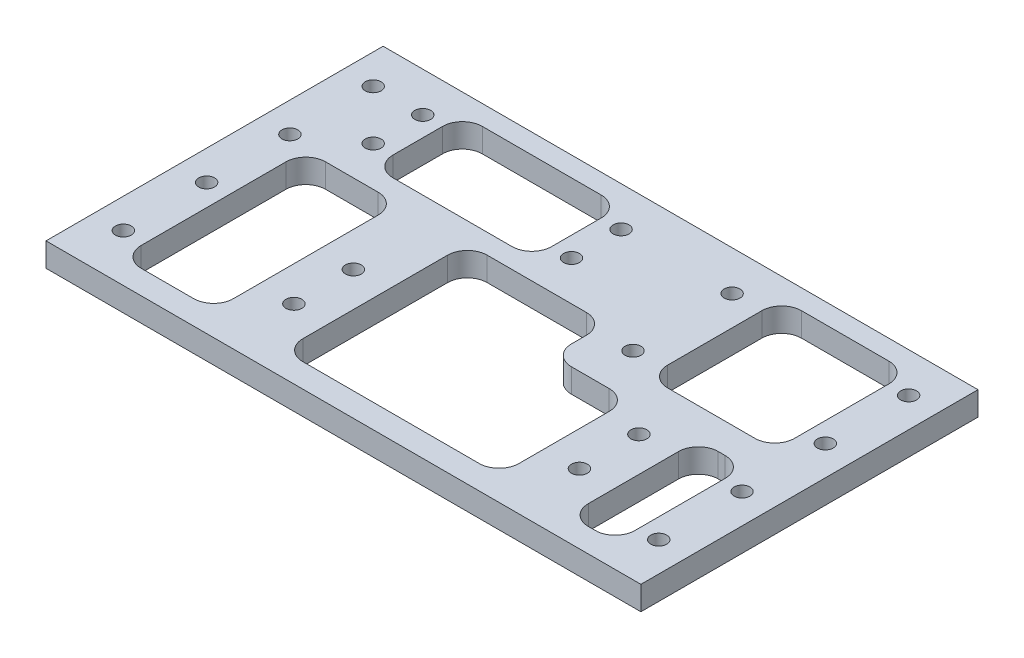
SolidWorks part; units mm, degrees
material "6061-T6 (SS)"
ref_plane "Front Plane" through (0, 0, 0) normal (0, 0, 1) x (1, 0, 0)
ref_plane "Top Plane" through (0, 0, 0) normal (0, 1, 0) x (1, 0, 0)
ref_plane "Right Plane" through (0, 0, 0) normal (1, 0, 0) x (0, 0, -1)
sketch "Sketch1" plane through (0, 0, 0) normal (0, 1, 0) x (1, 0, 0)
  line L1 (-150, 85) -> (150, 85)
  line L2 (-150, 85) -> (-150, -85)
  line L3 (-150, -85) -> (150, -85)
  line L4 (150, 85) -> (150, -85)
  line L5 (-150, 85) -> (150, -85) construction
  line L6 (-150, -85) -> (150, 85) construction
  point P0 (0, 0)
  dimension "D1" = 170
  dimension "D2" = 300
extrude "Boss-Extrude1" add sketch "Sketch1" along normal blind 12
sketch "Sketch2" plane through (0, 12, 0) normal (0, 1, 0) x (1, 0, 0)
  line L0 (0, 158.459) -> (0, -191.7487) construction
  line L1 (150, 85) -> (-150, 85) construction
  line L2 (-150, 85) -> (-150, -85) construction
  circle A0 centre (-135, 65) radius 4
  circle A1 centre (-135, 23) radius 4
  circle A2 centre (-135, -19) radius 4
  circle A3 centre (-135, -61) radius 4
  circle A4 centre (-135, -103) radius 4
  circle A5 centre (-135, -145) radius 4
  dimension "D3" = 8
  dimension "D1" = 20
  dimension "D2" = 15
  dimension "D4" = 6
  dimension "D5" = 15
extrude "Cut-Extrude1" cut sketch "Sketch2" against normal through all
mirror "Mirror1" about plane through (0, 0, 0) normal (1, 0, 0) of "Cut-Extrude1"
sketch "Sketch4" plane through (0, 12, 0) normal (0, 1, 0) x (1, 0, 0)
  line L0 (150, 85) -> (-150, 85) construction
  line L1 (-150, 85) -> (-150, -85) construction
  line L2 (150, -85) -> (150, 85) construction
  circle A0 centre (-110, 65) radius 4
  circle A1 centre (-10, 65) radius 4
  circle A2 centre (-110, 40) radius 4
  circle A3 centre (-10, 40) radius 4
  circle A4 centre (46, 65) radius 4
  circle A5 centre (46, 15) radius 4
  dimension "D1" = 8
  dimension "D6" = 8
  dimension "D2" = 25
  dimension "D3" = 100
  dimension "D4" = 20
  dimension "D5" = 40
  dimension "D7" = 20
  dimension "D8" = 104
  dimension "D9" = 50
extrude "Cut-Extrude2" cut sketch "Sketch4" against normal through all
sketch "Sketch5" plane through (0, 12, 0) normal (0, 1, 0) x (1, 0, 0)
  line L8 (-150, -85) -> (150, -85) construction
  line L9 (-150, 85) -> (-150, -85) construction
  circle A9 centre (-60, -20) radius 4
  circle A10 centre (-60, -50) radius 4
  circle A11 centre (84, -20) radius 4
  circle A12 centre (84, -50) radius 4
  dimension "D9" = 144
  dimension "D10" = 8
  dimension "D16" = 8
  dimension "D3" = 35
  dimension "D4" = 90
  dimension "D8" = 30
extrude "Cut-Extrude3" cut sketch "Sketch5" against normal through all
sketch "Sketch6" plane through (0, 12, 0) normal (0, 1, 0) x (1, 0, 0)
  line L0 (-150, 85) -> (-150, -85) construction
  line L1 (-67.5, -7.5) -> (-52.5, -7.5)
  line L2 (-67.5, -7.5) -> (-67.5, -62.5)
  line L3 (-67.5, -62.5) -> (-52.5, -62.5)
  line L4 (-52.5, -7.5) -> (-52.5, -62.5)
  line L5 (-67.5, -7.5) -> (-52.5, -62.5) construction
  line L6 (-67.5, -62.5) -> (-52.5, -7.5) construction
  line L7 (-150, -85) -> (150, -85) construction
  line L8 (150, 85) -> (-150, 85) construction
  line L9 (76.5, -7.5) -> (91.5, -7.5)
  line L10 (76.5, -7.5) -> (76.5, -62.5)
  line L11 (76.5, -62.5) -> (91.5, -62.5)
  line L12 (91.5, -7.5) -> (91.5, -62.5)
  line L13 (76.5, -7.5) -> (91.5, -62.5) construction
  line L14 (76.5, -62.5) -> (91.5, -7.5) construction
  line L15 (61, 75) -> (125, 75)
  line L16 (-65, 30) -> (-65, -7.5)
  line L17 (-55, 30) -> (-55, -7.5)
  line L18 (-60, 52.5) -> (-60, -35) construction
  line L19 (-124, 20) -> (-77.5, 20)
  line L20 (84, -20) -> (84, -50) construction
  line L21 (101.5, -7.5) -> (125, -7.5)
  line L22 (61, 75) -> (61, 7.5)
  line L23 (61, 7.5) -> (125, 7.5)
  line L24 (125, 75) -> (125, 7.5)
  line L25 (-77.5, 20) -> (-77.5, -73)
  line L26 (-100, 75) -> (-20, 75)
  line L27 (-100, 75) -> (-100, 30)
  line L28 (-100, 30) -> (-20, 30)
  line L29 (-20, 75) -> (-20, 30)
  line L30 (-100, 75) -> (-20, 30) construction
  line L31 (-100, 30) -> (-20, 75) construction
  line L32 (-124, 20) -> (-124, -73)
  line L33 (-124, -73) -> (-77.5, -73)
  line L34 (-42.5, 20) -> (27.5, 20)
  line L35 (27.5, 20) -> (27.5, -7.5)
  line L36 (27.5, -7.5) -> (66.5, -7.5)
  line L37 (66.5, -7.5) -> (66.5, -73)
  line L38 (66.5, -73) -> (-42.5, -73)
  line L39 (-42.5, -73) -> (-42.5, 20)
  line L40 (101.5, -7.5) -> (101.5, -73)
  line L41 (101.5, -73) -> (125, -73)
  line L42 (-65, -62.5) -> (-65, -73)
  line L43 (-65, -73) -> (-55, -73)
  line L44 (-55, -73) -> (-55, -62.5)
  line L45 (125, -7.5) -> (125, -73)
  line L73 (150, -85) -> (150, 85) construction
  circle A0 centre (46, 65) radius 4 construction
  point P0 (-60, -35)
  point P9 (84, -35)
  point P27 (-60, 52.5)
  dimension "D1" = 90
  dimension "D15" = 15
  dimension "D11" = 15
  dimension "D2" = 15
  dimension "D3" = 55
  dimension "D4" = 50
  dimension "D6" = 55
  dimension "D7" = 15
  dimension "D8" = 10
  dimension "D9" = 80
  dimension "D10" = 45
  dimension "D12" = 10
  dimension "D13" = 5
  dimension "D14" = 12
  dimension "D16" = 10
  dimension "D17" = 10
  dimension "D18" = 10
  dimension "D20" = 10
  dimension "D21" = 25
  dimension "D22" = 10
  dimension "D24" = 10
  dimension "D25" = 5
  dimension "D26" = 26
  dimension "D27" = 70
extrude "Cut-Extrude4" cut sketch "Sketch6" against normal through all
fillet "Fillet1" radius 10 22 edges at (125, 6, -75) (61, 6, -75) (125, 6, -7.5) (61, 6, -7.5) (-42.5, 6, 73) (66.5, 6, 73) (66.5, 6, 7.5) (27.5, 6, 7.5) (27.5, 6, -20) (-42.5, 6, -20) (-124, 6, 73) (-77.5, 6, 73) (-77.5, 6, -20) (-124, 6, -20) (-100, 6, -30) (-20, 6, -30) (-20, 6, -75) (-100, 6, -75) (125, 6, 73) (101.5, 6, 73) (125, 6, 7.5) (101.5, 6, 7.5)
